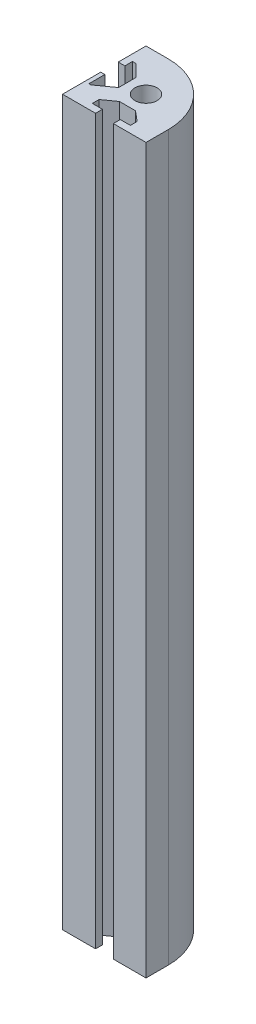
SolidWorks part; units mm, degrees
ref_plane "Front" through (0, 0, 0) normal (0, 0, 1) x (1, 0, 0)
ref_plane "Top" through (0, 0, 0) normal (0, 1, 0) x (1, 0, 0)
ref_plane "Right" through (0, 0, 0) normal (1, 0, 0) x (0, 0, -1)
sketch "Croquis1" plane through (0, 0, 0) normal (0, 1, 0) x (1, 0, 0)
  line L0 (-7, 15) -> (-15, 15)
  line L1 (-15, 15) -> (15, 15) construction
  line L2 (-15, 15) -> (-15, -15) construction
  line L3 (-15, -15) -> (15, -15) construction
  line L4 (15, 15) -> (15, -15) construction
  line L5 (-15, 15) -> (15, -15) construction
  line L6 (-15, -15) -> (15, 15) construction
  line L7 (-15, 15) -> (-15, 5.0276)
  line L8 (-15, 5.0276) -> (-12.6234, 5.0276)
  line L9 (-12.6234, 5.0276) -> (-12.6234, 7.7527)
  line L10 (-12.6234, 7.7527) -> (-11.3205, 7.7527)
  line L11 (-11.3205, 7.7527) -> (-7, 3.4321)
  line L12 (-7, 3.4321) -> (-7, -2.8611)
  line L13 (-7, -2.8611) -> (-12.793, -7)
  line L14 (-12.793, -7) -> (-13.5273, -7)
  line L15 (-13.5273, -7) -> (-13.5273, -1.258)
  line L16 (-13.5273, -1.258) -> (-15, -1.258)
  line L17 (-15, -1.258) -> (-15, -15)
  line L18 (-15, -15) -> (-3.1399, -15)
  line L19 (-3.1399, -15) -> (-3.1399, -12.5058)
  line L20 (-3.1399, -12.5058) -> (-6.779, -12.5058)
  line L21 (-6.779, -12.5058) -> (-6.779, -10.0798)
  line L22 (-6.779, -10.0798) -> (-2.5129, -7.0319)
  line L23 (-2.5129, -7.0319) -> (3.2559, -7.0319)
  line L24 (3.2559, -7.0319) -> (6.8949, -10.0798)
  line L25 (6.8949, -10.0798) -> (6.8949, -12.5058)
  line L26 (6.8949, -12.5058) -> (3.2559, -12.5058)
  line L27 (3.2559, -12.5058) -> (3.2559, -15)
  line L28 (3.2559, -15) -> (15, -15)
  line L29 (15, -15) -> (15, -7)
  line L30 (0, 0) -> (-50000, 0) construction
  line L31 (0, 0) -> (0, -50000) construction
  circle A0 centre (0, 0) radius 4
  arc A1 (-7, 15) -> (15, -7) centre (-7, -7) cw
  point P0 (0, 0)
  dimension "D3" = 8
  dimension "D4" = 22
  dimension "D1" = 30
  dimension "D2" = 30
extrude "Saliente-Extruir1" add sketch "Croquis1" along normal blind 260
